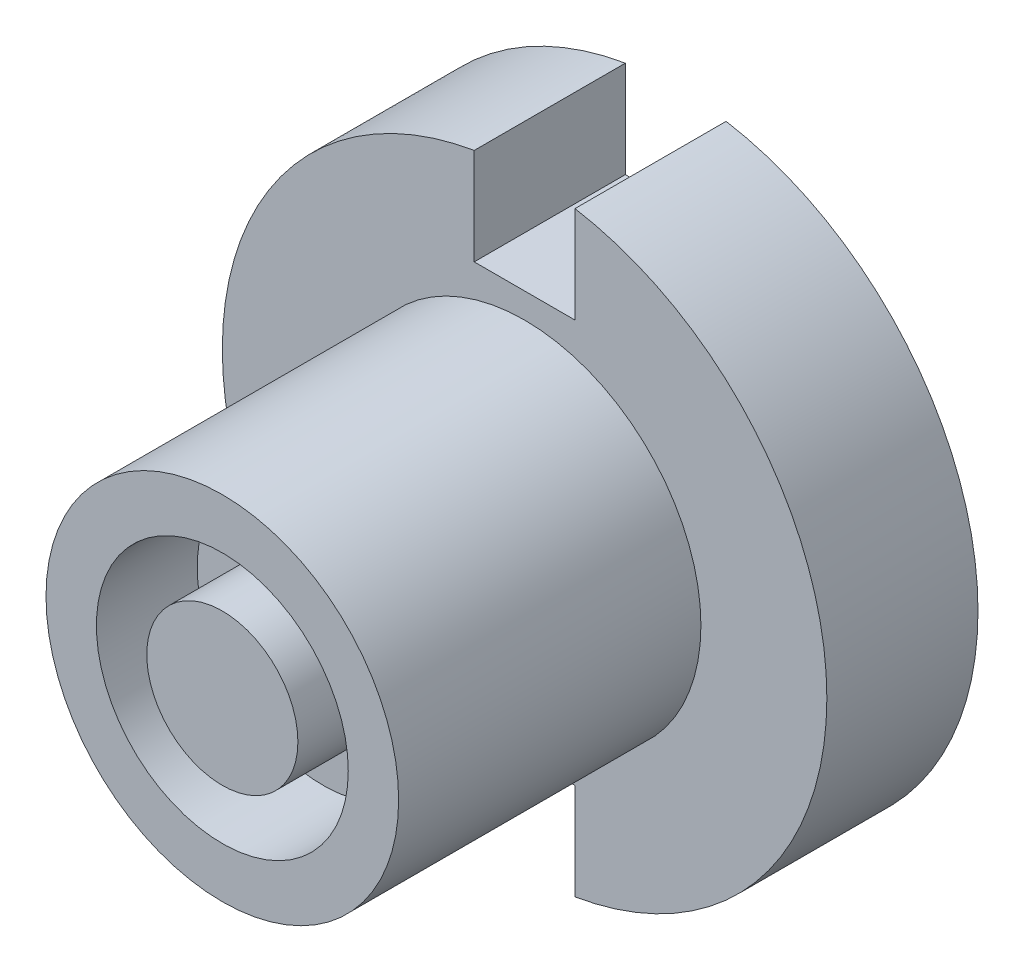
SolidWorks part; units mm, degrees
material "Caucho"
ref_plane "Alzado" through (0, 0, 0) normal (0, 0, 1) x (1, 0, 0)
ref_plane "Planta" through (0, 0, 0) normal (0, 1, 0) x (1, 0, 0)
ref_plane "Vista lateral" through (0, 0, 0) normal (1, 0, 0) x (0, 0, -1)
sketch "Croquis1" plane through (0, 0, 0) normal (0, 0, 1) x (1, 0, 0)
  circle A0 centre (-4.7541, 3.9783) radius 3.5
  dimension "D1" = 7
extrude "Saliente-Extruir1" add sketch "Croquis1" along normal blind 6
sketch "Croquis2" plane through (0, 0, 0) normal (0, 0, -1) x (-1, 0, 0)
  circle A0 centre (4.7541, 3.9783) radius 6
  dimension "D1" = 12
extrude "Saliente-Extruir2" add sketch "Croquis2" along normal blind 3
sketch "Croquis3" plane through (0, 0, 6) normal (0, 0, 1) x (1, 0, 0)
  line L0 (-4.7541, 7.4783) -> (-4.7541, 0.4783) construction
  circle A0 centre (-4.7541, 3.9783) radius 3.5 construction
  circle A1 centre (-4.7541, 3.9783) radius 3.5 construction
  circle A2 centre (-4.7541, 3.9783) radius 2.5
  circle A3 centre (-4.7541, 3.9783) radius 1.5
  point P10 (-4.7541, 1.4783)
  dimension "D1" = 1
  dimension "D3" = 3
  dimension "D2" = 1
extrude "Cortar-Extruir1" cut sketch "Croquis3" against normal blind 2
sketch "Croquis4" plane through (0, 0, 0) normal (0, 0, 1) x (1, 0, 0)
  line L0 (-4.7541, 9.9783) -> (-4.7541, -2.0217) construction
  line L1 (-5.7541, 7.9783) -> (-3.7541, 7.9783)
  line L2 (-3.7541, 7.9783) -> (-3.7541, 9.9783)
  line L3 (-5.7541, 7.9783) -> (-5.7541, 9.9783)
  line L4 (-3.7541, 9.9783) -> (-5.7541, 9.9783)
  line L5 (-5.7541, -0.0217) -> (-3.7541, -0.0217)
  line L6 (-3.7541, -0.0217) -> (-3.7541, -2.0217)
  line L7 (-5.7541, -0.0217) -> (-5.7541, -2.0217)
  line L8 (-3.7541, -2.0217) -> (-4.7541, -2.0217)
  line L9 (-5.7541, -2.0217) -> (-4.7541, -2.0217)
  circle A0 centre (-4.7541, 3.9783) radius 6 construction
  circle A2 centre (-4.7541, 3.9783) radius 3.5 construction
  circle A3 centre (-4.7541, 3.9783) radius 3.5 construction
  point P8 (-4.7541, 7.9783)
  point P10 (-4.7541, 9.9783)
  point P14 (-4.7541, -0.0217)
  dimension "D1" = 2
  dimension "D2" = 2
  dimension "D3" = 2
  dimension "D4" = 2
  dimension "D5" = 4
  dimension "D6" = 4
extrude "Cortar-Extruir2" cut sketch "Croquis4" against normal through all
